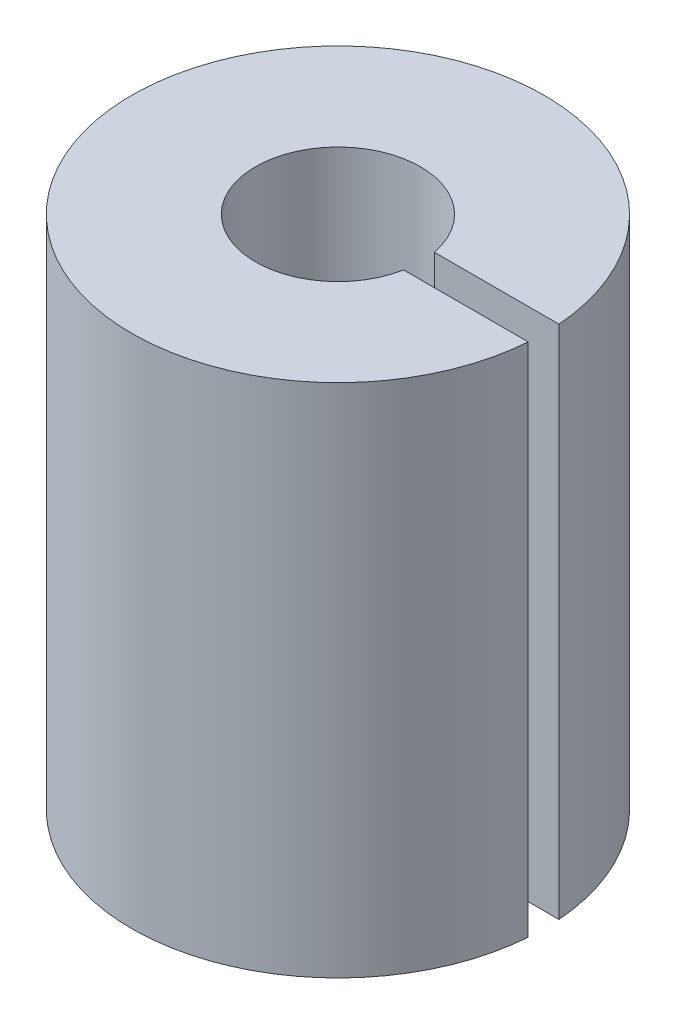
SolidWorks part; units mm, degrees
ref_plane "Plan de face" through (0, 0, 0) normal (0, 0, 1) x (1, 0, 0)
ref_plane "Plan de dessus" through (0, 0, 0) normal (0, 1, 0) x (1, 0, 0)
ref_plane "Plan de droite" through (0, 0, 0) normal (1, 0, 0) x (0, 0, -1)
sketch "Esquisse2" plane through (0, 0, 0) normal (0, 1, 0) x (1, 0, 0)
  circle A0 centre (0, 0) radius 5
  circle A1 centre (0, 0) radius 10
  dimension "D1" = 20
extrude "Boss.-Extru.1" add sketch "Esquisse2" along normal blind 25 contours A1
sketch "Sketch1" plane through (0, 25, 0) normal (0, 1, 0) x (1, 0, 0)
  circle A0 centre (0, 0) radius 4
  dimension "D1" = 8
extrude "Cut-Extrude1" cut sketch "Sketch1" against normal blind 12.5
sketch "Sketch2" plane through (0, 0, 0) normal (0, -1, 0) x (1, 0, 0)
  circle A0 centre (0, 0) radius 2.5
  dimension "D1" = 5
extrude "Cut-Extrude2" cut sketch "Sketch2" against normal blind 12.5
sketch "Sketch3" plane through (0, 25, 0) normal (0, 1, 0) x (1, 0, 0)
  line L0 (0, 0.7445) -> (0, -0.7445)
  line L1 (0, 0.7445) -> (12.4347, 0.7445)
  line L3 (0, -0.7445) -> (12.4347, -0.7445)
  line L4 (12.4347, 0.7445) -> (12.4347, -0.7445)
  line L5 (0, 0) -> (12.4347, 0) construction
  point P0 (0, 0)
extrude "Cut-Extrude3" cut sketch "Sketch3" against normal blind 25
